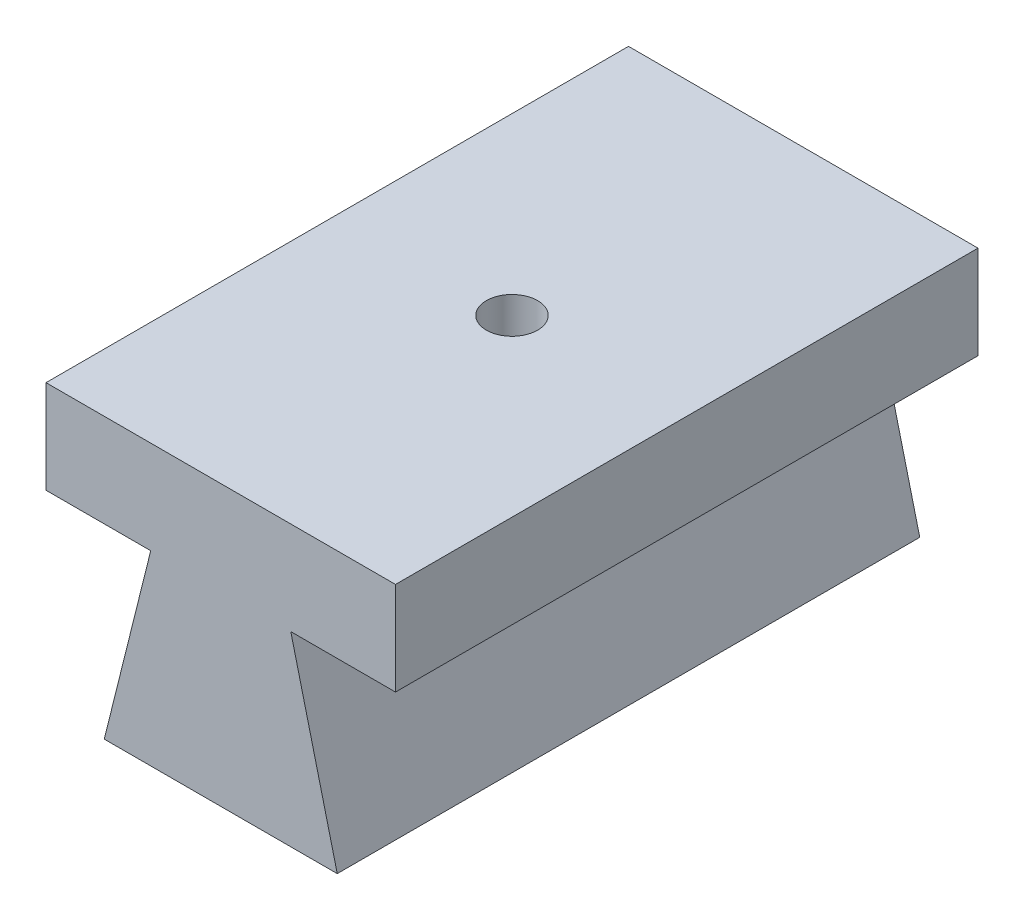
SolidWorks part; units mm, degrees
ref_plane "Front" through (0, 0, 0) normal (0, 0, 1) x (1, 0, 0)
ref_plane "Top" through (0, 0, 0) normal (0, 1, 0) x (1, 0, 0)
ref_plane "Right" through (0, 0, 0) normal (1, 0, 0) x (0, 0, -1)
sketch "Sketch1" plane through (0, 0, 0) normal (0, 0, 1) x (1, 0, 0)
  line L0 (0, 0) -> (0, 26.1543) construction
  line L1 (6.35, 0) -> (-6.35, 0)
  line L2 (-6.35, 0) -> (-3.8168, 10.16)
  line L3 (6.35, 0) -> (3.8168, 10.16)
  line L4 (-3.8168, 10.16) -> (-9.525, 10.16)
  line L5 (3.8168, 10.16) -> (9.525, 10.16)
  line L6 (-9.525, 10.16) -> (-9.525, 15.24)
  line L7 (9.525, 10.16) -> (9.525, 15.24)
  line L8 (-9.525, 15.24) -> (9.525, 15.24)
  point P5 (0, 0)
  point P13 (0, 15.24)
  dimension "D1" = 19.05
  dimension "D2" = 5.08
  dimension "D3" = 10.16
  dimension "D4" = 12.7
  dimension "D5" = 28
extrude "Base-Extrude" add sketch "Sketch1" along normal mid plane 31.75
sketch "Sketch3" plane through (0, 15.24, 0) normal (0, 1, 0) x (-1, 0, 0)
  circle A0 centre (0, 0) radius 1.397
  dimension "D1" = 2.794
extrude "Cut-Extrude2" cut sketch "Sketch3" against normal blind 12.7
